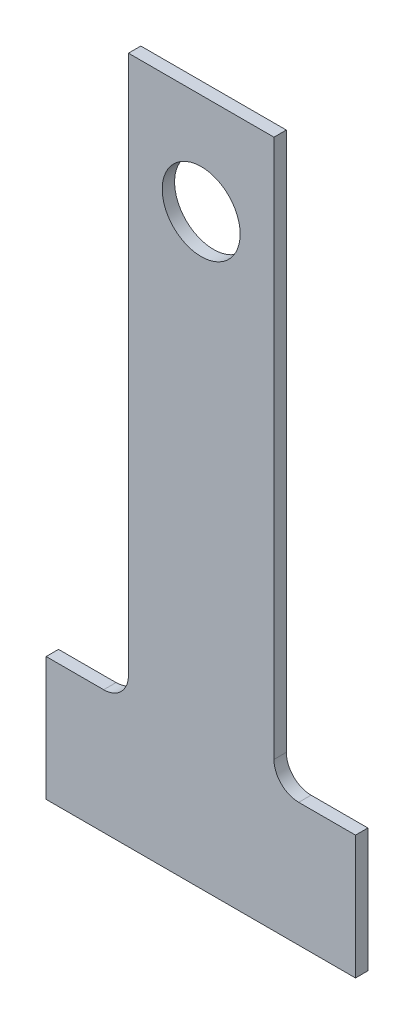
SolidWorks part; units mm, degrees
material "Nikiel"
ref_plane "Płaszczyzna przednia" through (0, 0, 0) normal (0, 0, 1) x (1, 0, 0)
ref_plane "Płaszczyzna górna" through (0, 0, 0) normal (0, 1, 0) x (1, 0, 0)
ref_plane "Płaszczyzna prawa" through (0, 0, 0) normal (1, 0, 0) x (0, 0, -1)
sketch "Szkic1" plane through (0, 0, 0) normal (0, 0, 1) x (1, 0, 0)
  line L6 (-12.5, -6) -> (-12.5, -16)
  line L10 (-12.5, -16) -> (12.5, -16)
  line L11 (12.5, -16) -> (12.5, -6)
  line L12 (7.91, -6) -> (12.5, -6)
  line L13 (-7.85, -6) -> (-12.5, -6)
  line L20 (-5.85, -4) -> (-5.85, 5.45)
  line L22 (5.91, 5.45) -> (5.91, -4)
  line L32 (-5.85, 5.45) -> (-5.85, 39.55)
  line L33 (-5.85, 39.55) -> (5.91, 39.55)
  line L34 (5.91, 39.55) -> (5.91, 5.45)
  arc A0 (-5.85, -4) -> (-7.85, -6) centre (-7.85, -4) cw
  arc A5 (5.91, -4) -> (7.91, -6) centre (7.91, -4) ccw
  point P0 (0, 0)
  dimension "D1" = 2
  dimension "D2" = 25
  dimension "D3" = 10
extrude "Dodanie-wyciągnięcie1" add sketch "Szkic1" along normal blind 1
sketch "Szkic2" plane through (0, 0, 1) normal (0, 0, 1) x (1, 0, 0)
  circle A18 centre (0.03, 31.4) radius 3.15
extrude "Wytnij-wyciągnięcie1" cut sketch "Szkic2" against normal blind 1
